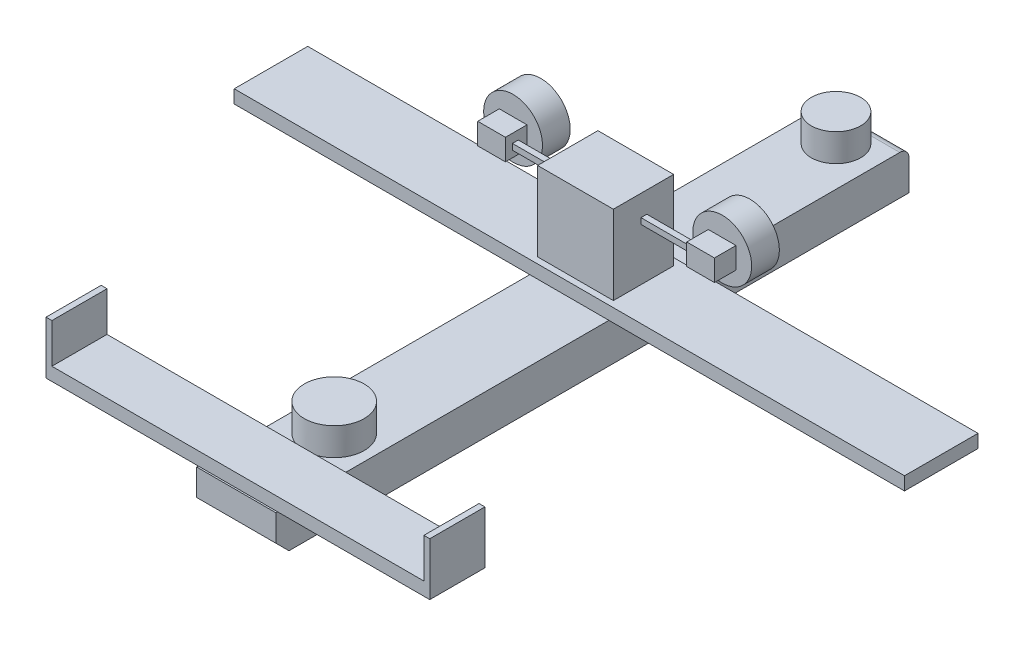
SolidWorks part; units mm, degrees
ref_plane "Front Plane" through (0, 0, 0) normal (0, 0, 1) x (1, 0, 0)
ref_plane "Top Plane" through (0, 0, 0) normal (0, 1, 0) x (1, 0, 0)
ref_plane "Right Plane" through (0, 0, 0) normal (1, 0, 0) x (0, 0, -1)
sketch "Sketch1" plane through (0, 0, 0) normal (0, 0, 1) x (1, 0, 0)
  line L1 (-76.2, -38.1) -> (76.2, -38.1)
  line L2 (-76.2, -38.1) -> (-76.2, 38.1)
  line L3 (-76.2, 38.1) -> (76.2, 38.1)
  line L4 (76.2, -38.1) -> (76.2, 38.1)
  line L5 (-76.2, -38.1) -> (76.2, 38.1) construction
  line L6 (-76.2, 38.1) -> (76.2, -38.1) construction
  point P0 (0, 0)
  dimension "D1" = 152.4
  dimension "D2" = 76.2
extrude "Boss-Extrude1" add sketch "Sketch1" along normal blind 1219.2
fillet "Fillet1" radius 17.78 1 edges at (0, 38.1, 0)
chamfer "Chamfer1" distance 25.4 angle 45 1 edges at (0, -38.1, 1219.2)
sketch "Sketch2" plane through (0, 38.1, 0) normal (0, 1, 0) x (1, 0, 0)
  line L0 (0, 0) -> (0, -1304.1747) construction
  line L1 (0, -507.0125) -> (152.4, -507.0125) construction
  line L2 (-76.2, -1219.2) -> (-76.2, -17.78) construction
  line L3 (-645.2388, -577.7691) -> (645.2388, -577.7691)
  line L4 (-645.2388, -577.7691) -> (-645.2388, -436.2559)
  line L5 (-645.2388, -436.2559) -> (645.2388, -436.2559)
  line L6 (645.2388, -577.7691) -> (645.2388, -436.2559)
  line L7 (-645.2388, -577.7691) -> (645.2388, -436.2559) construction
  line L8 (-645.2388, -436.2559) -> (645.2388, -577.7691) construction
  line L9 (-369.4404, -1215.9583) -> (369.4404, -1215.9583)
  line L10 (-369.4404, -1215.9583) -> (-369.4404, -1109.7731)
  line L11 (-369.4404, -1109.7731) -> (369.4404, -1109.7731)
  line L12 (369.4404, -1215.9583) -> (369.4404, -1109.7731)
  line L13 (-369.4404, -1215.9583) -> (369.4404, -1109.7731) construction
  line L14 (-369.4404, -1109.7731) -> (369.4404, -1215.9583) construction
  circle A0 centre (0, -1162.8657) radius 53.0926
  circle A1 centre (0, -93.9736) radius 57.2365
  circle A2 centre (76.2, -507.0125) radius 55.4729
  circle A3 centre (-76.2, -507.0125) radius 55.4729
  point P9 (0, -1162.8657)
  point P22 (-76.2, -507.0125)
  line M12 (76.2, -1219.2) -> (76.2, -17.78)
  line M14 (-76.2, -17.78) -> (-76.2, -1219.2)
extrude "Boss-Extrude2" add sketch "Sketch2" along normal blind 25.4 contours A2 L3 L6 L5 M12 | A3 L5 L4 L3 M14 | A3 L3 A2 L5 M14 M12 | L10 L9 L12 L11
sketch "Sketch3" plane through (0, 63.5, 0) normal (0, 1, 0) x (1, 0, 0)
  line L1 (-72.9402, -449.9138) -> (72.9402, -449.9138)
  line L2 (-72.9402, -449.9138) -> (-72.9402, -565.9877)
  line L3 (-72.9402, -565.9877) -> (72.9402, -565.9877)
  line L4 (72.9402, -449.9138) -> (72.9402, -565.9877)
  line L5 (-72.9402, -449.9138) -> (72.9402, -565.9877) construction
  line L6 (-72.9402, -565.9877) -> (72.9402, -449.9138) construction
  point P0 (0, -507.9508)
extrude "Boss-Extrude3" add sketch "Sketch3" along normal blind 152.4 contours L2 L1 L4 L3
sketch "Sketch4" plane through (-72.9402, 0, 0) normal (-1, 0, 0) x (0, 0, 1)
  line L1 (501.557, 175.3217) -> (512.8856, 175.3217)
  line L2 (501.557, 175.3217) -> (501.557, 163.993)
  line L3 (501.557, 163.993) -> (512.8856, 163.993)
  line L4 (512.8856, 175.3217) -> (512.8856, 163.993)
  line L5 (501.557, 175.3217) -> (512.8856, 163.993) construction
  line L6 (501.557, 163.993) -> (512.8856, 175.3217) construction
  point P0 (507.2213, 169.6574)
extrude "Boss-Extrude4" add sketch "Sketch4" along normal blind 101.6 contours L2 L1 L4 L3
sketch "Sketch5" plane through (-174.5402, 0, 0) normal (-1, 0, 0) x (0, 0, 1)
  line L1 (484.8054, 192.2685) -> (526.3409, 192.2685)
  line L2 (484.8054, 192.2685) -> (484.8054, 151.2621)
  line L3 (484.8054, 151.2621) -> (526.3409, 151.2621)
  line L4 (526.3409, 192.2685) -> (526.3409, 151.2621)
  line L5 (484.8054, 192.2685) -> (526.3409, 151.2621) construction
  line L6 (484.8054, 151.2621) -> (526.3409, 192.2685) construction
  point P0 (505.5731, 171.7653)
extrude "Boss-Extrude5" add sketch "Sketch5" along normal blind 53.34
sketch "Sketch6" plane through (0, 0, 484.8054) normal (0, 0, -1) x (-1, 0, 0)
  circle A0 centre (201.3378, 173.0083) radius 56.6605
extrude "Boss-Extrude6" add sketch "Sketch6" along normal blind 53.34
mirror "Mirror1" about plane through (0, 0, 0) normal (1, 0, 0) of "Boss-Extrude4", "Boss-Extrude5", "Boss-Extrude6"
sketch "Sketch7" plane through (0, 38.1, 0) normal (0, 1, 0) x (1, 0, 0)
  circle A0 centre (0, -64.4201) radius 47.5324
  circle A1 centre (0, -1030.4766) radius 57.7119
extrude "Boss-Extrude7" add sketch "Sketch7" along normal blind 53.34
sketch "Sketch8" plane through (0, 63.5, 0) normal (0, 1, 0) x (1, 0, 0)
  line L0 (-369.4404, -1109.7731) -> (369.4404, -1109.7731) construction
  line L1 (369.4404, -1109.7731) -> (358.1295, -1109.7731)
  line L2 (369.4404, -1109.7731) -> (369.4404, -1215.9583)
  line L3 (369.4404, -1215.9583) -> (358.1295, -1215.9583)
  line L4 (358.1295, -1109.7731) -> (358.1295, -1215.9583)
  line L5 (369.4404, -1215.9583) -> (369.4404, -1109.7731) construction
  line L6 (-369.4404, -1215.9583) -> (369.4404, -1215.9583) construction
extrude "Boss-Extrude8" add sketch "Sketch8" along normal blind 76.2 contours L2 L1 L4 L3
mirror "Mirror2" about plane through (0, 0, 0) normal (1, 0, 0) of "Boss-Extrude8"
